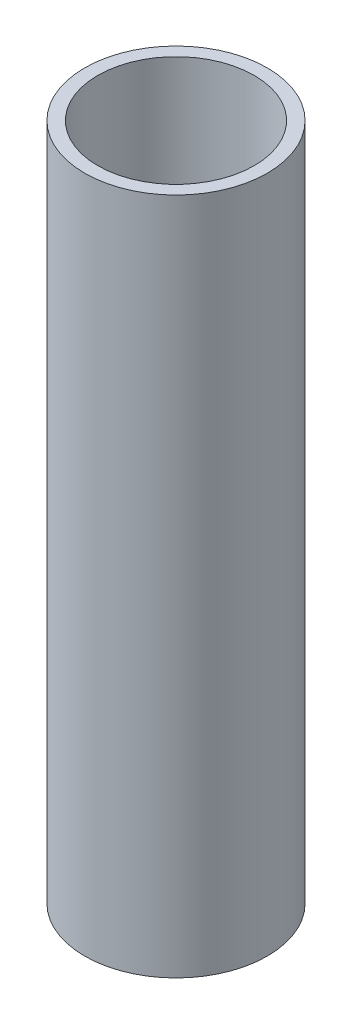
SolidWorks part; units mm, degrees
ref_plane "Front Plane" through (0, 0, 0) normal (0, 0, 1) x (1, 0, 0)
ref_plane "Top Plane" through (0, 0, 0) normal (0, 1, 0) x (1, 0, 0)
ref_plane "Right Plane" through (0, 0, 0) normal (1, 0, 0) x (0, 0, -1)
sketch "Sketch1" plane through (0, 0, 0) normal (0, 1, 0) x (1, 0, 0)
  circle A0 centre (0, 0) radius 44.45
  circle A1 centre (0, 0) radius 38.1
  dimension "D1" = 88.9
  dimension "D2" = 76.2
extrude "Boss-Extrude1" add sketch "Sketch1" along normal blind 330.2
